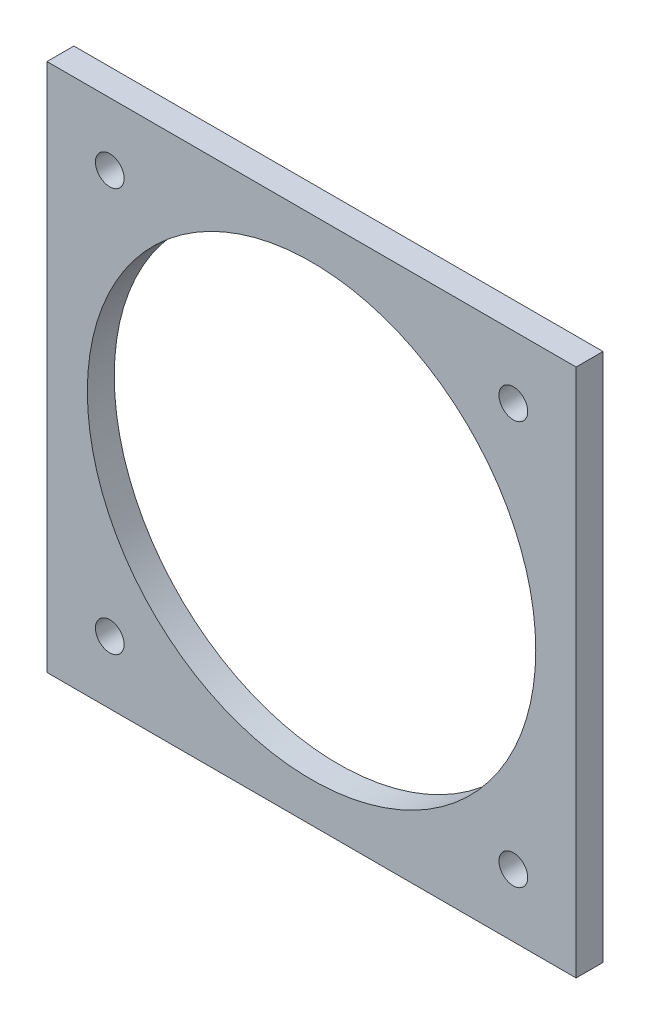
SolidWorks part; units mm, degrees
ref_plane "Ebene vorne" through (0, 0, 0) normal (0, 0, 1) x (1, 0, 0)
ref_plane "Ebene oben" through (0, 0, 0) normal (0, 1, 0) x (1, 0, 0)
ref_plane "Ebene rechts" through (0, 0, 0) normal (1, 0, 0) x (0, 0, -1)
sketch "Skizze1" plane through (0, 0, 0) normal (0, 0, 1) x (1, 0, 0)
  line L1 (0, 0) -> (59, 0)
  line L2 (0, 0) -> (0, 59)
  line L3 (0, 59) -> (59, 59)
  line L4 (59, 0) -> (59, 59)
  circle A0 centre (7, 52) radius 1.6
  circle A1 centre (52, 52) radius 1.6
  circle A2 centre (52, 7) radius 1.6
  circle A3 centre (7, 7) radius 1.6
  circle A4 centre (29.5, 29.4) radius 25
  dimension "D3" = 3.2
  dimension "D8" = 3.2
  dimension "D9" = 3.2
  dimension "D14" = 3.2
  dimension "D15" = 50
  dimension "D1" = 59
  dimension "D2" = 59
  dimension "D4" = 7
  dimension "D5" = 7
  dimension "D6" = 7
  dimension "D7" = 7
  dimension "D10" = 7
  dimension "D11" = 7
  dimension "D12" = 7
  dimension "D13" = 7
  dimension "D16" = 29.6
  dimension "D17" = 29.5
extrude "Aufsatz-Linear austragen1" add sketch "Skizze1" along normal blind 3
